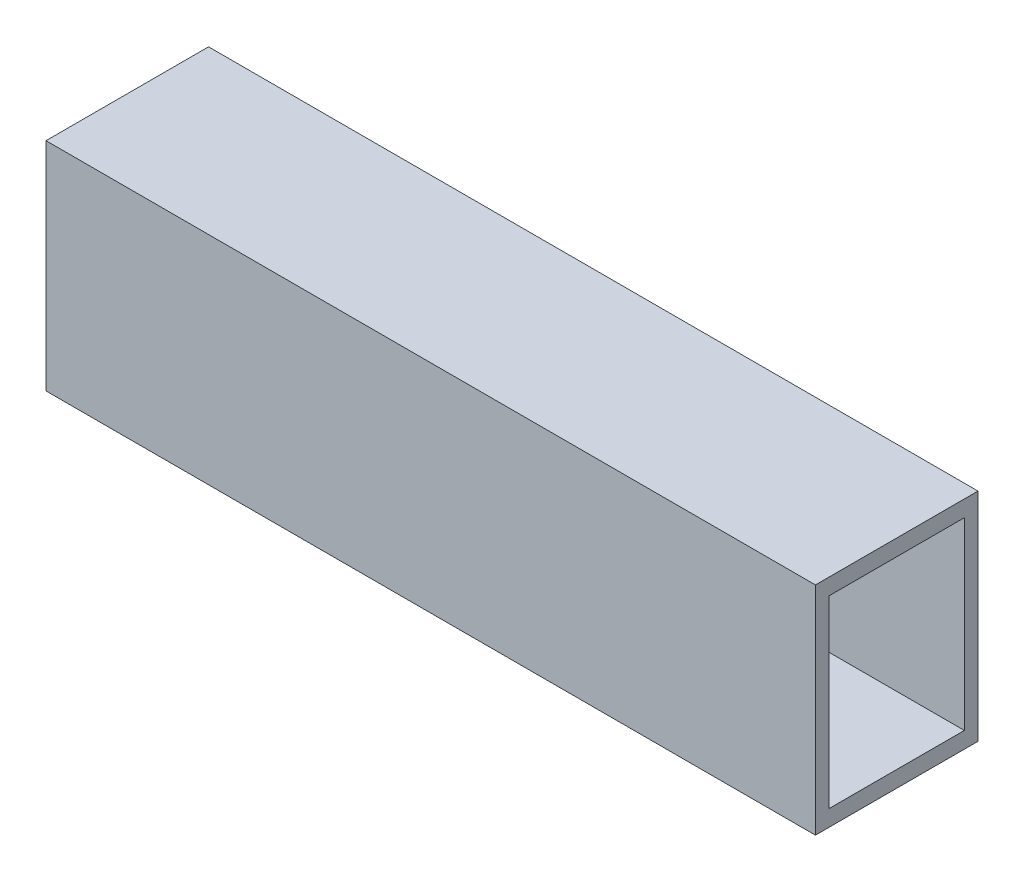
SolidWorks part; units mm, degrees
ref_plane "Front Plane" through (0, 0, 0) normal (0, 0, 1) x (1, 0, 0)
ref_plane "Top Plane" through (0, 0, 0) normal (0, 1, 0) x (1, 0, 0)
ref_plane "Right Plane" through (0, 0, 0) normal (1, 0, 0) x (0, 0, -1)
sketch "Croquis1" plane through (0, 0, 0) normal (1, 0, 0) x (0, 0, -1)
  line L0 (-15, -20) -> (-15, 20)
  line L1 (-15, -20) -> (15, -20)
  line L2 (-15, 20) -> (15, 20)
  line L3 (15, -20) -> (15, 20)
  line L4 (-15, -20) -> (15, 20) construction
  line L5 (-15, 20) -> (15, -20) construction
  line L6 (-12.4805, -17) -> (-12.4805, 17)
  line L7 (-12.4805, -17) -> (12.4805, -17)
  line L8 (-12.4805, 17) -> (12.4805, 17)
  line L9 (12.4805, -17) -> (12.4805, 17)
  line L10 (-12.4805, -17) -> (12.4805, 17) construction
  line L11 (-12.4805, 17) -> (12.4805, -17) construction
  point P0 (-15, 0)
  point P1 (0, 0)
  point P2 (0, 0)
  dimension "D1" = 40
  dimension "D2" = 30
  dimension "D3" = 3
  dimension "D4" = 2.5195
extrude "Saliente-Extruir1" add sketch "Croquis1" along normal blind 142
